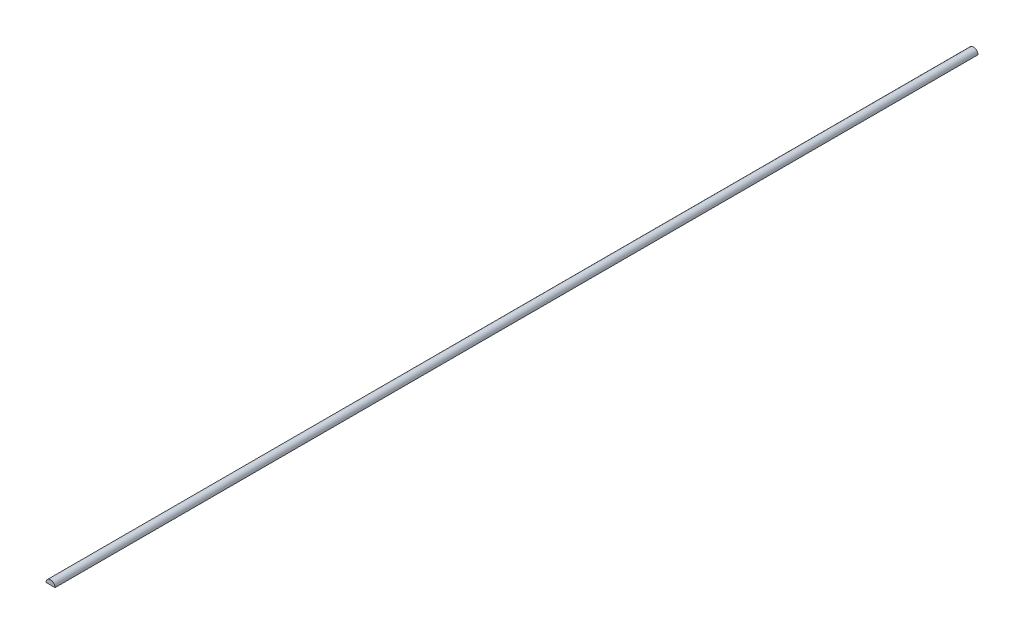
SolidWorks part; units mm, degrees
material "Acrylic (Medium-high impact)"
ref_plane "Front" through (0, 0, 0) normal (0, 0, 1) x (1, 0, 0)
ref_plane "Top" through (0, 0, 0) normal (0, 1, 0) x (1, 0, 0)
ref_plane "Right" through (0, 0, 0) normal (1, 0, 0) x (0, 0, -1)
sketch "Sketch1" plane through (0, 0, 0) normal (0, 0, 1) x (1, 0, 0)
  line L0 (-1, 0) -> (1, 0)
  arc A0 (1, 0) -> (-1, 0) centre (0, 0) ccw
  dimension "D1" = 2
extrude "Extrude1" add sketch "Sketch1" along normal mid plane 203.9
